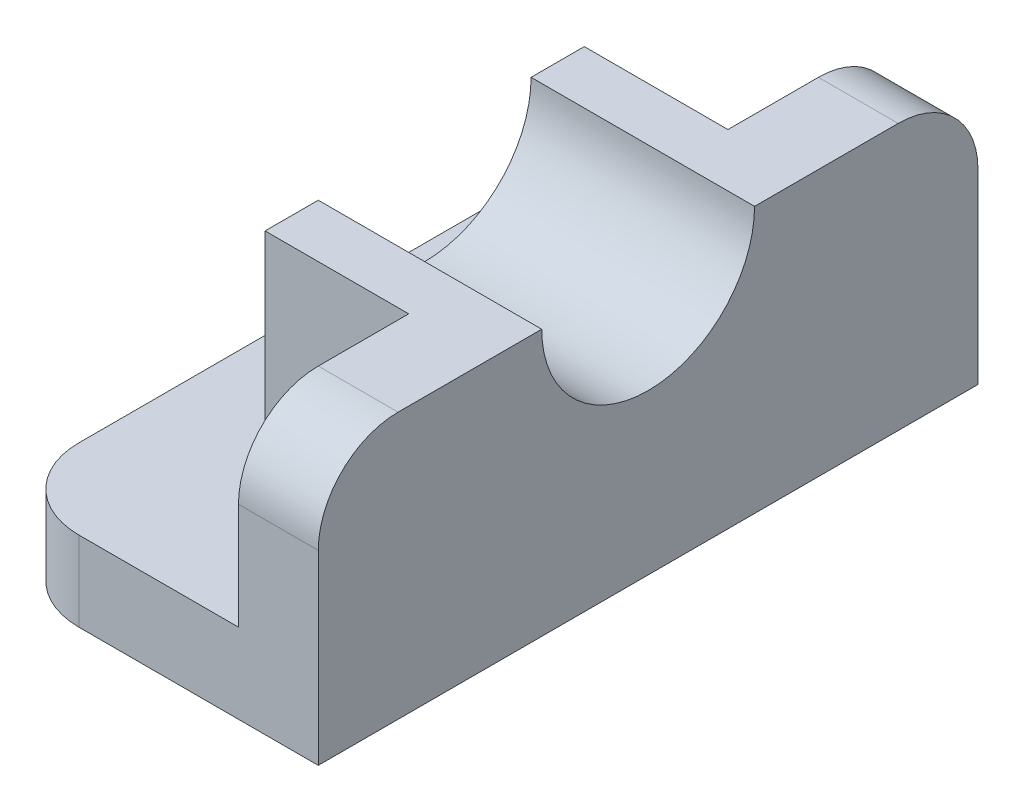
SolidWorks part; units mm, degrees
ref_plane "Front Plane" through (0, 0, 0) normal (0, 0, 1) x (1, 0, 0)
ref_plane "Top Plane" through (0, 0, 0) normal (0, 1, 0) x (1, 0, 0)
ref_plane "Right Plane" through (0, 0, 0) normal (1, 0, 0) x (0, 0, -1)
sketch "Sketch1" plane through (0, 0, 0) normal (0, 0, 1) x (1, 0, 0)
  line L0 (0, 0) -> (60, 0)
  line L1 (60, 0) -> (60, 50)
  line L2 (60, 50) -> (45, 50)
  line L3 (45, 50) -> (45, 15)
  line L4 (45, 15) -> (0, 15)
  line L5 (0, 15) -> (0, 0)
  dimension "D1" = 60
  dimension "D2" = 50
  dimension "D3" = 15
extrude "Boss-Extrude2" add sketch "Sketch1" along normal blind 124
fillet "Fillet1" radius 15 3 edges at (52.5, 50, 0) (0, 7.5, 124) (52.5, 50, 124)
fillet "Fillet2" radius 15 1 edges at (0, 7.5, 0)
sketch "Sketch2" plane through (45, 0, 0) normal (-1, 0, 0) x (0, 0, 1)
  line L1 (124, 15) -> (0, 15) construction
  line L2 (32, 50) -> (92, 50)
  line L3 (32, 50) -> (32, 15)
  line L4 (32, 15) -> (92, 15)
  line L5 (92, 50) -> (92, 15)
  line L6 (109, 50) -> (15, 50) construction
  point P0 (76.9737, 50)
  dimension "D1" = 60
  dimension "D2" = 32
extrude "Boss-Extrude3" add sketch "Sketch2" along normal blind 27
sketch "Sketch5" plane through (18, 0, 0) normal (-1, 0, 0) x (0, 0, 1)
  line L0 (92, 50) -> (32, 50) construction
  circle A0 centre (62, 50) radius 20
  dimension "D1" = 40
extrude "Cut-Extrude8" cut sketch "Sketch5" against normal blind 50
